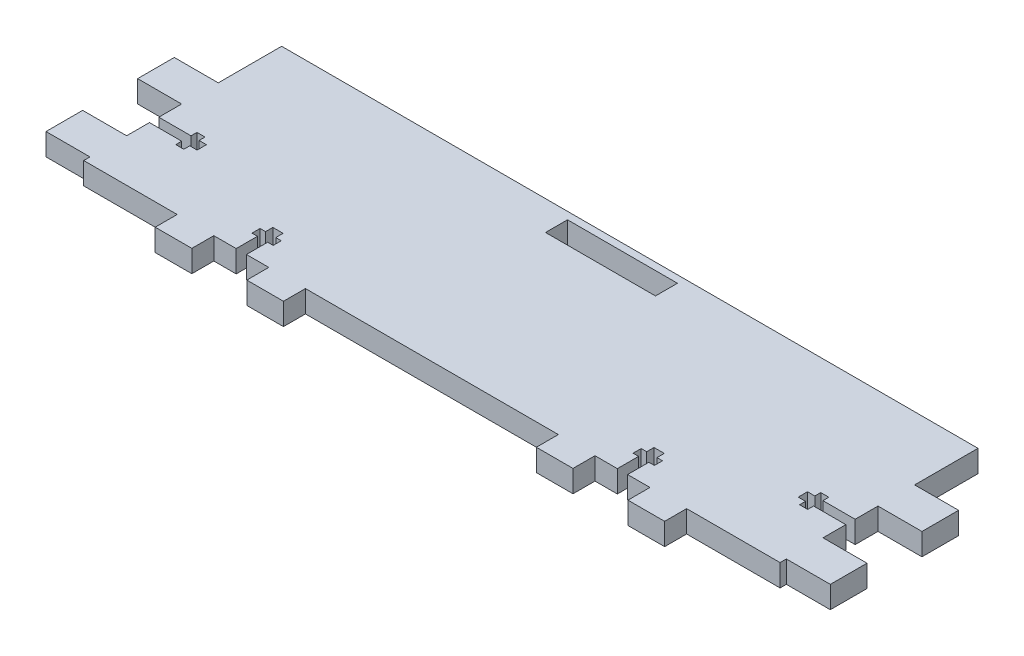
SolidWorks part; units mm, degrees
ref_plane "Front" through (0, 0, 0) normal (0, 0, 1) x (1, 0, 0)
ref_plane "Top" through (0, 0, 0) normal (0, 1, 0) x (1, 0, 0)
ref_plane "Right" through (0, 0, 0) normal (1, 0, 0) x (0, 0, -1)
sketch "Эскиз1" plane through (0, 0, 0) normal (0, 1, 0) x (1, 0, 0)
  line L0 (-131.8881, 0) -> (137.6783, 0) construction
  line L2 (-95, 23) -> (-95, 13.7093)
  line L3 (-95, -23) -> (-69.5, -23)
  line L4 (95, 23) -> (95, 13.7093)
  line L5 (-95, 23) -> (95, -23) construction
  line L6 (-95, -23) -> (95, 23) construction
  line L7 (0, 62.5664) -> (0, -52.5944) construction
  line L8 (69.5, 51.8234) -> (69.5, -44.3584) construction
  line L9 (59.5, 51.8234) -> (59.5, -44.3584) construction
  line L10 (34.5, 51.8234) -> (34.5, -44.3584) construction
  line L11 (44.5, 51.8234) -> (44.5, -44.3584) construction
  line L12 (106.5886, -29) -> (-1.3442, -29) construction
  line L13 (59.5, -23) -> (59.5, -29)
  line L14 (59.5, -29) -> (69.5, -29)
  line L15 (69.5, -29) -> (69.5, -23)
  line L16 (34.5, -23) -> (34.5, -29)
  line L17 (34.5, -29) -> (44.5, -29)
  line L18 (44.5, -29) -> (44.5, -23)
  line L19 (52, -9.9523) -> (52, -35.233) construction
  line L20 (44.5, -23) -> (50.6, -23)
  line L21 (69.5, -23) -> (95, -23)
  line L22 (102.7865, -17.2) -> (39.4134, -17.2) construction
  line L23 (103.2055, -15) -> (39.8324, -15) construction
  line L24 (103.3102, -13) -> (39.9371, -13) construction
  line L25 (50.6, -27.2711) -> (50.6, -9.9523) construction
  line L26 (49.1, -27.2711) -> (49.1, -9.9523) construction
  line L27 (50.6, -23) -> (50.6, -17.2)
  line L28 (50.6, -17.2) -> (49.1, -17.2)
  line L29 (49.1, -17.2) -> (49.1, -15)
  line L30 (49.1, -15) -> (50.6, -15)
  line L31 (50.6, -15) -> (50.6, -13)
  line L32 (50.6, -13) -> (53.4, -13)
  line L33 (53.4, -23) -> (53.4, -17.2)
  line L34 (53.4, -17.2) -> (54.9, -17.2)
  line L35 (54.9, -17.2) -> (54.9, -15)
  line L36 (54.9, -15) -> (53.4, -15)
  line L37 (53.4, -15) -> (53.4, -13)
  line L38 (53.4, -23) -> (59.5, -23)
  line L39 (-50.6, -17.2) -> (-49.1, -17.2)
  line L40 (-49.1, -17.2) -> (-49.1, -15)
  line L41 (-49.1, -15) -> (-50.6, -15)
  line L42 (-50.6, -15) -> (-50.6, -13)
  line L43 (-50.6, -13) -> (-53.4, -13)
  line L44 (-53.4, -15) -> (-53.4, -13)
  line L45 (-54.9, -15) -> (-53.4, -15)
  line L46 (-54.9, -17.2) -> (-54.9, -15)
  line L47 (-53.4, -17.2) -> (-54.9, -17.2)
  line L48 (-53.4, -23) -> (-53.4, -17.2)
  line L49 (-50.6, -23) -> (-50.6, -17.2)
  line L50 (-34.5, -23) -> (-34.5, -29)
  line L51 (-34.5, -29) -> (-44.5, -29)
  line L52 (-44.5, -29) -> (-44.5, -23)
  line L53 (-59.5, -23) -> (-59.5, -29)
  line L54 (-59.5, -29) -> (-69.5, -29)
  line L55 (-69.5, -29) -> (-69.5, -23)
  line L56 (-59.5, -23) -> (-53.4, -23)
  line L57 (-50.6, -23) -> (-44.5, -23)
  line L58 (-34.5, -23) -> (34.5, -23)
  line L59 (107, 23) -> (107, -23) construction
  line L66 (119.5315, -21.2907) -> (95, -21.2907) construction
  line L67 (95, -21.2907) -> (107, -21.2907)
  line L68 (107, -21.2907) -> (107, -11.2907)
  line L69 (107, -11.2907) -> (95, -11.2907)
  line L70 (119.5315, 3.7093) -> (89.9629, 3.7093) construction
  line L71 (95, 3.7093) -> (107, 3.7093)
  line L72 (107, 3.7093) -> (107, 13.7093)
  line L73 (107, 13.7093) -> (95, 13.7093)
  line L74 (95, 3.7093) -> (95, -2.519)
  line L75 (95, -21.2907) -> (95, -23)
  line L76 (119.5315, -3.7907) -> (75.4928, -3.7907) construction
  line L77 (111.868, -2.519) -> (75.4928, -2.519) construction
  line L78 (111.868, -0.9012) -> (75.4928, -0.9012) construction
  line L79 (82, 3.0697) -> (82, -8.7695) construction
  line L80 (84, 3.0697) -> (84, -8.7695) construction
  line L81 (86.2, 3.0697) -> (86.2, -8.7695) construction
  line L82 (82, -5.0625) -> (82, -2.519)
  line L83 (82, -2.519) -> (84, -2.519)
  line L84 (84, -2.519) -> (84, -0.9012)
  line L85 (84, -0.9012) -> (86.2, -0.9012)
  line L86 (86.2, -0.9012) -> (86.2, -2.519)
  line L87 (86.2, -2.519) -> (95, -2.519)
  line L88 (82, -5.0625) -> (84, -5.0625)
  line L89 (84, -5.0625) -> (84, -6.6803)
  line L90 (84, -6.6803) -> (86.2, -6.6803)
  line L91 (86.2, -6.6803) -> (86.2, -5.0625)
  line L92 (86.2, -5.0625) -> (95, -5.0625)
  line L93 (95, -5.0625) -> (95, -11.2907)
  line L94 (-84, -6.6803) -> (-86.2, -6.6803)
  line L95 (-84, -5.0625) -> (-84, -6.6803)
  line L96 (-82, -5.0625) -> (-84, -5.0625)
  line L97 (-82, -5.0625) -> (-82, -2.519)
  line L98 (-82, -2.519) -> (-84, -2.519)
  line L99 (-84, -2.519) -> (-84, -0.9012)
  line L100 (-84, -0.9012) -> (-86.2, -0.9012)
  line L101 (-86.2, -0.9012) -> (-86.2, -2.519)
  line L102 (-86.2, -6.6803) -> (-86.2, -5.0625)
  line L103 (-86.2, -5.0625) -> (-95, -5.0625)
  line L104 (-86.2, -2.519) -> (-95, -2.519)
  line L105 (-95, -21.2907) -> (-107, -21.2907)
  line L106 (-107, -21.2907) -> (-107, -11.2907)
  line L107 (-107, -11.2907) -> (-95, -11.2907)
  line L108 (-95, 3.7093) -> (-107, 3.7093)
  line L109 (-107, 3.7093) -> (-107, 13.7093)
  line L110 (-107, 13.7093) -> (-95, 13.7093)
  line L111 (-95, 3.7093) -> (-95, -2.519)
  line L112 (-95, -5.0625) -> (-95, -11.2907)
  line L113 (-95, -21.2907) -> (-95, -23)
  line L114 (-95, 23) -> (-95, 31)
  line L115 (-95, 31) -> (95, 31)
  line L116 (95, 31) -> (95, 23)
  line L118 (-15, 29) -> (15, 29)
  line L119 (-15, 29) -> (-15, 23)
  line L120 (-15, 23) -> (15, 23)
  line L121 (15, 29) -> (15, 23)
  point P0 (0, 0)
  point P47 (49.85, -15)
  point P53 (52, -13)
  point P57 (-49.85, -15)
  point P75 (0, 18)
  point P113 (82, -3.7907)
  dimension "D2" = 190
  dimension "D3" = 25.5
  dimension "D4" = 10
  dimension "D5" = 15
  dimension "D6" = 10
  dimension "D7" = 6
  dimension "D8" = 7.5
  dimension "D9" = 10
  dimension "D10" = 2
  dimension "D11" = 2.2
  dimension "D12" = 1.4
  dimension "D13" = 1.5
  dimension "D16" = 2
  dimension "D17" = 12
  dimension "D18" = 10
  dimension "D19" = 15
  dimension "D20" = 10
  dimension "D21" = 7.5
  dimension "D22" = 13
  dimension "D23" = 2
  dimension "D24" = 2.2
  dimension "D25" = 8
  dimension "D26" = 6
  dimension "D27" = 30
extrude "Бобышка-Вытянуть1" add sketch "Эскиз1" along normal blind 6
